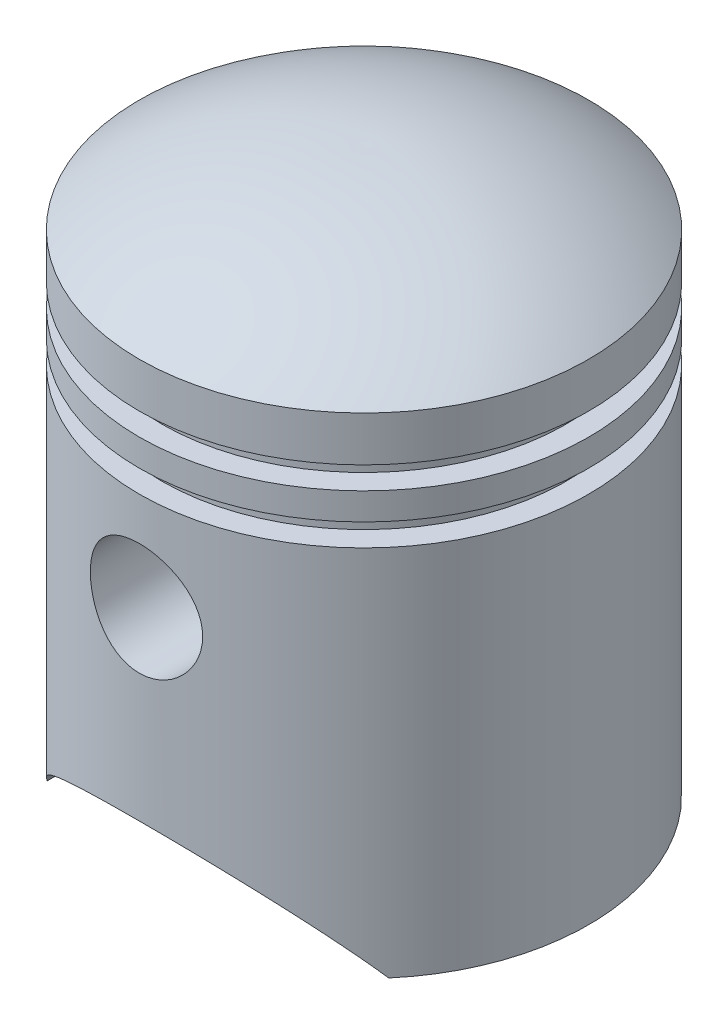
SolidWorks part; units mm, degrees
ref_plane "Front Plane" through (0, 0, 0) normal (0, 0, 1) x (1, 0, 0)
ref_plane "Top Plane" through (0, 0, 0) normal (0, 1, 0) x (1, 0, 0)
ref_plane "Right Plane" through (0, 0, 0) normal (1, 0, 0) x (0, 0, -1)
sketch "Sketch1" plane through (0, 0, 0) normal (0, 0, 1) x (1, 0, 0)
  line L0 (25, 0) -> (25, 41.5)
  line L1 (25, 49.5) -> (22.5, 49.5)
  line L2 (22.5, 49.5) -> (22.5, 47)
  line L3 (22.5, 47) -> (25, 47)
  line L4 (25, 44) -> (22.5, 44)
  line L5 (22.5, 44) -> (22.5, 41.5)
  line L6 (22.5, 41.5) -> (25, 41.5)
  line L7 (25, 49.5) -> (25, 54.5)
  line L8 (25, 44) -> (25, 47)
  line L9 (23, 0) -> (23, 39.5)
  line L10 (20.5, 39.5) -> (23, 39.5)
  line L11 (20.5, 45.5) -> (20.5, 39.5)
  line L12 (20.5, 45.5) -> (20.5, 45.5)
  line L13 (20.5, 45.5) -> (20.5, 45.5)
  line L14 (20.5, 45.5) -> (20.5, 45.5)
  line L15 (20.5, 51.5) -> (20.5, 45.5)
  line L16 (23, 51.5) -> (20.5, 51.5)
  line L17 (23, 51.5) -> (23, 53.4845)
  line L18 (23, 0) -> (25, 0)
  line L19 (0, 62.5) -> (0, 60.5006)
  line L20 (0, 60.5006) -> (0.0492, 60.5006)
  arc A0 (25, 54.5) -> (0, 62.5) centre (0.9839, 22.5121) ccw
  arc A1 (23, 53.4845) -> (0.0492, 60.5006) centre (0.9839, 22.5121) ccw
  dimension "D3" = 40
  dimension "D1" = 25
  dimension "D2" = 62.5
  dimension "D4" = 54.5
  dimension "D5" = 5
  dimension "D6" = 2.5
  dimension "D7" = 2.5
  dimension "D8" = 2.5
  dimension "D9" = 2.5
  dimension "D10" = 3
  dimension "D11" = 2
revolve "Revolve2" add sketch "Sketch1" angle 360 about L19
sketch "Sketch3" plane through (0, 0, 0) normal (0, 0, 1) x (1, 0, 0)
  line L0 (-25, 0) -> (25, 0) construction
  line L1 (-19, 0) -> (19, 0)
  circle A0 centre (0, 30.5) radius 6.25
  arc A1 (-19, 0) -> (19, 0) centre (0, -13.05) cw
  point P8 (0, 62.5)
  point P12 (0, 10)
  dimension "D1" = 12.5
  dimension "D2" = 32
  dimension "D3" = 38
  dimension "D4" = 10
extrude "Cut-Extrude2" cut sketch "Sketch3" against normal through all both and the other way through all
sketch "Sketch4" plane through (0, 0, 0) normal (0, 0, 1) x (1, 0, 0)
  circle A0 centre (0, 30.5) radius 6.25
  circle A1 centre (0, 30.5) radius 7.25
extrude "Boss-Extrude1" add sketch "Sketch4" along normal up to surface (12.2061 mm away) from offset 12
mirror "Mirror1" about plane through (0, 0, 0) normal (0, 0, 1) of "Boss-Extrude1"
